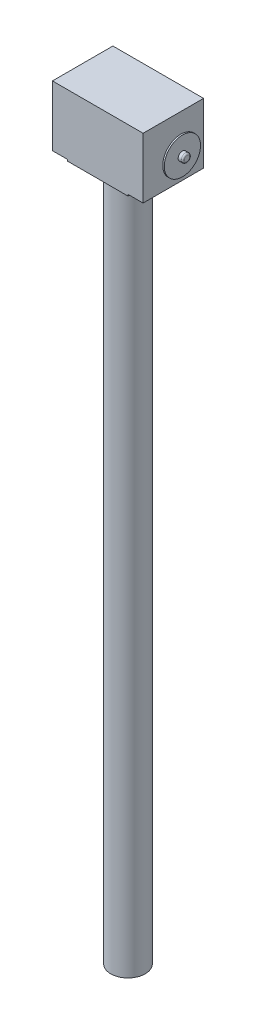
SolidWorks part; units mm, degrees
ref_plane "Front Plane" through (0, 0, 0) normal (0, 0, 1) x (1, 0, 0)
ref_plane "Top Plane" through (0, 0, 0) normal (0, 1, 0) x (1, 0, 0)
ref_plane "Right Plane" through (0, 0, 0) normal (1, 0, 0) x (0, 0, -1)
sketch "Sketch1" plane through (0, 0, 0) normal (0, 1, 0) x (1, 0, 0)
  line L0 (-150, 100) -> (150, -100) construction
  line L1 (-150, 100) -> (150, 100)
  line L2 (-150, 100) -> (-150, -100)
  line L3 (-150, -100) -> (150, -100)
  line L4 (150, 100) -> (150, -100)
  dimension "D1" = 300
  dimension "D2" = 200
extrude "Boss-Extrude1" add sketch "Sketch1" along normal blind 200
sketch "Sketch2" plane through (150, 0, 0) normal (1, 0, 0) x (0, 0, -1)
  line L0 (100, 200) -> (-100, 0) construction
  circle A0 centre (0, 100) radius 14
  dimension "D1" = 28
extrude "Boss-Extrude2" add sketch "Sketch2" along normal blind 25
sketch "Sketch3" plane through (175, 0, 0) normal (1, 0, 0) x (0, 0, -1)
  circle A0 centre (0, 100) radius 60
  dimension "D1" = 120
extrude "Boss-Extrude3" add sketch "Sketch3" along normal blind 5
sketch "Sketch4" plane through (180, 0, 0) normal (1, 0, 0) x (0, 0, -1)
  circle A0 centre (0, 100) radius 14
  dimension "D1" = 28
extrude "Boss-Extrude4" add sketch "Sketch4" along normal blind 15
fillet "Fillet1" radius 5 1 edges at (195, 100, -14)
sketch "Sketch5" plane through (0, 0, 0) normal (0, -1, 0) x (1, 0, 0)
  line L0 (150, 100) -> (-150, -100) construction
  line L1 (-150, 100) -> (150, 100) construction
  line L2 (-100, 100) -> (100, 100)
  line L3 (-100, 100) -> (-100, -100)
  line L4 (-100, -100) -> (100, -100)
  line L5 (100, 100) -> (100, -100)
  line L6 (150, -100) -> (-150, -100) construction
  line L7 (-100, 100) -> (100, -100) construction
  dimension "D1" = 200
extrude "Boss-Extrude5" add sketch "Sketch5" along normal blind 5
sketch "Sketch6" plane through (0, -5, 0) normal (0, -1, 0) x (1, 0, 0)
  circle A0 centre (0, 0) radius 57
  dimension "D1" = 114
extrude "Boss-Extrude6" add sketch "Sketch6" along normal blind 2300
